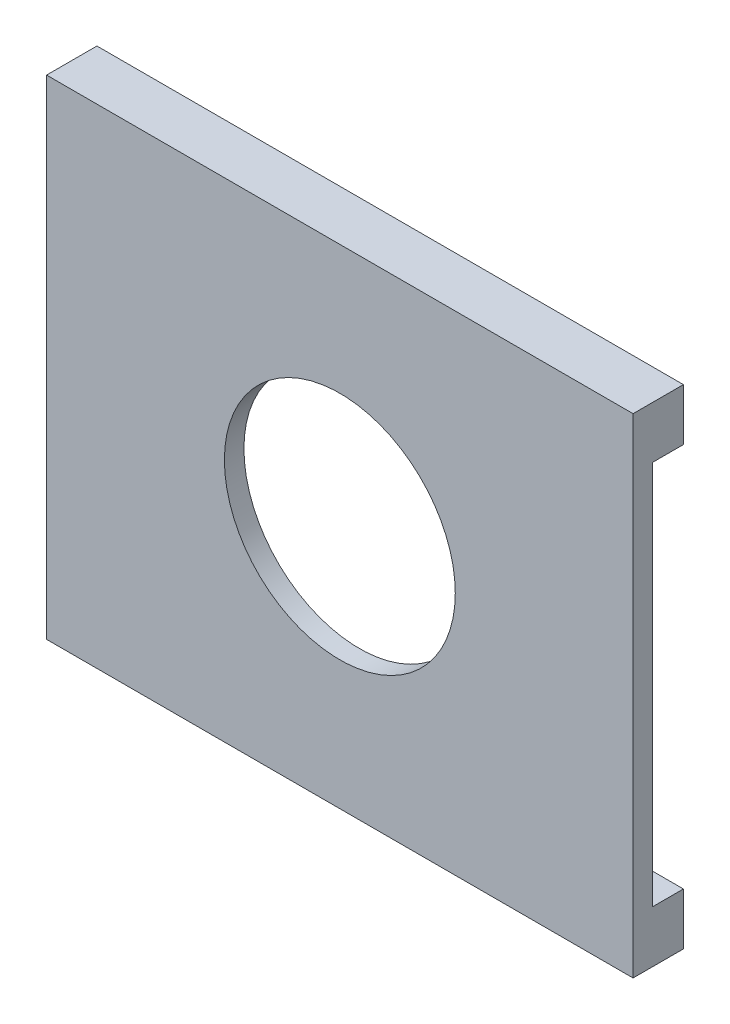
SolidWorks part; units mm, degrees
ref_plane "Front" through (0, 0, 0) normal (0, 0, 1) x (1, 0, 0)
ref_plane "Top" through (0, 0, 0) normal (0, 1, 0) x (1, 0, 0)
ref_plane "Right" through (0, 0, 0) normal (1, 0, 0) x (0, 0, -1)
sketch "Sketch1" plane through (0, 0, 0) normal (0, 0, 1) x (1, 0, 0)
  line L1 (0, 0) -> (76.2, 0)
  line L2 (0, 0) -> (0, 63.5)
  line L3 (0, 63.5) -> (76.2, 63.5)
  line L4 (76.2, 0) -> (76.2, 63.5)
extrude "Boss-Extrude1" add sketch "Sketch1" along normal blind 2.54
ref_plane "Plane1" through (0, 0, 0) normal (0, 0, -1) x (-1, 0, 0)
sketch "Sketch2" plane through (0, 0, 0) normal (0, 0, -1) x (-1, 0, 0)
  line L0 (0, 63.5) -> (0, 56.75)
  line L1 (0, 63.5) -> (0, 0) construction
  line L2 (0, 56.75) -> (-76.2, 56.75)
  line L3 (-76.2, 0) -> (-76.2, 63.5) construction
  line L4 (-76.2, 56.75) -> (-76.2, 63.5)
  line L5 (-76.2, 63.5) -> (0, 63.5)
  line L6 (0, 31.75) -> (-76.2, 31.75) construction
  line L7 (-76.2, 0) -> (0, 0)
  line L8 (-76.2, 6.75) -> (-76.2, 0)
  line L9 (0, 6.75) -> (-76.2, 6.75)
  line L10 (0, 0) -> (0, 6.75)
extrude "Boss-Extrude2" add sketch "Sketch2" along normal blind 4
ref_plane "Plane2" through (0, 0, -4) normal (0, 0, -1) x (-1, 0, 0)
sketch "Sketch3" plane through (0, 0, -4) normal (0, 0, -1) x (-1, 0, 0)
  line L0 (-76.2, 60.125) -> (0, 60.125) construction
  line L1 (-76.2, 63.5) -> (-76.2, 56.75) construction
  line L2 (0, 56.75) -> (0, 63.5) construction
  line L3 (-76.2, 31.75) -> (0, 31.75) construction
  line L4 (-76.2, 6.75) -> (-76.2, 56.75) construction
  line L5 (0, 56.75) -> (0, 6.75) construction
  line L6 (-38.1, 63.5) -> (-38.1, 0) construction
  line L7 (0, 63.5) -> (-76.2, 63.5) construction
  line L8 (-76.2, 0) -> (0, 0) construction
  circle A0 centre (-63.5, 60.125) radius 2.032
  circle A1 centre (-63.5, 3.375) radius 2.032
  circle A2 centre (-12.7, 3.375) radius 2.032
  circle A3 centre (-12.7, 60.125) radius 2.032
extrude "Cut-Extrude1" cut sketch "Sketch3" against normal blind 3.81
ref_plane "Plane3" through (0, 0, 2.54) normal (0, 0, 1) x (1, 0, 0)
sketch "Sketch4" plane through (0, 0, 2.54) normal (0, 0, 1) x (1, 0, 0)
  line L0 (0, 31.75) -> (76.2, 31.75) construction
  line L1 (0, 63.5) -> (0, 0) construction
  line L2 (76.2, 0) -> (76.2, 63.5) construction
  circle A0 centre (38.1, 31.75) radius 15
extrude "Cut-Extrude2" cut sketch "Sketch4" against normal blind 10
sketch "Sketch5" plane through (0, 0, 0) normal (0, 0, -1) x (-1, 0, 0)
  line L2 (-24.13, 56.75) -> (-27.94, 56.75)
  line L4 (-24.13, 6.75) -> (-27.94, 6.75)
  line L7 (-24.13, 46.59) -> (-24.13, 56.75)
  line L8 (-24.13, 56.75) -> (-24.2963, 56.7085)
  line L9 (-24.13, 46.59) -> (-27.94, 46.59)
  line L10 (-27.94, 46.59) -> (-27.94, 56.75)
  line L11 (-24.13, 16.91) -> (-27.94, 16.91)
  line L12 (-27.94, 16.91) -> (-27.94, 6.75)
  line L13 (-24.13, 16.91) -> (-24.13, 6.75)
extrude "Boss-Extrude3" add sketch "Sketch5" along normal blind 1.27 contours L13 L4 L12 L11 | L2 L10 L9 L7
